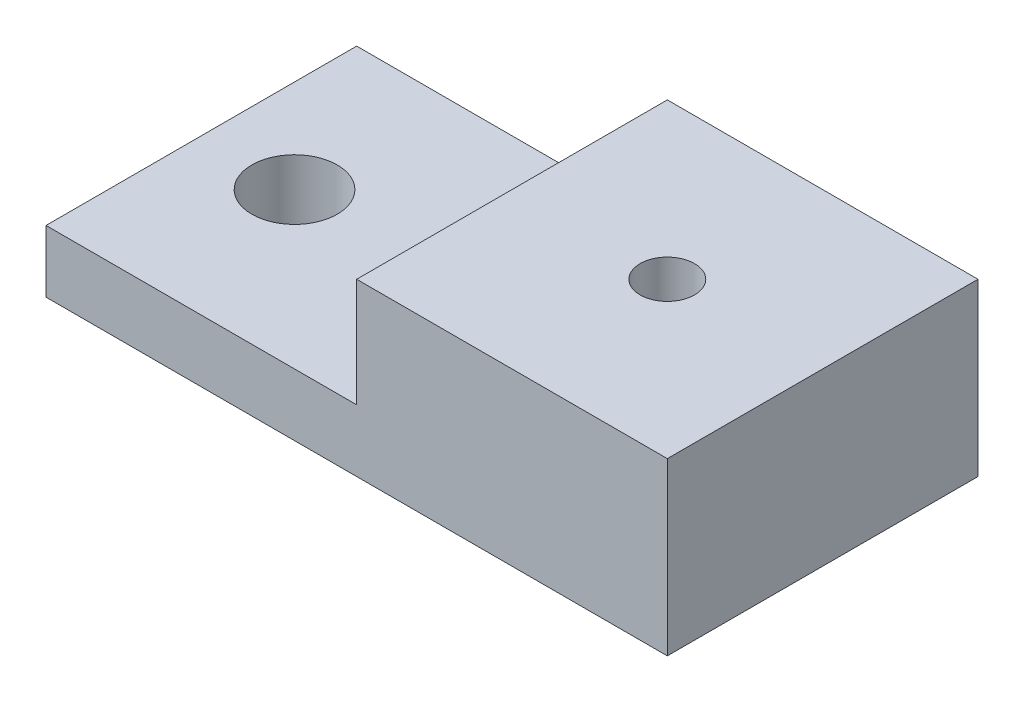
SolidWorks part; units mm, degrees
ref_plane "Front Plane" through (0, 0, 0) normal (0, 0, 1) x (1, 0, 0)
ref_plane "Top Plane" through (0, 0, 0) normal (0, 1, 0) x (1, 0, 0)
ref_plane "Right Plane" through (0, 0, 0) normal (1, 0, 0) x (0, 0, -1)
sketch "Sketch1" plane through (0, 0, 0) normal (0, 1, 0) x (1, 0, 0)
  line L0 (0, 10) -> (40, 10) construction
  line L1 (0, 0) -> (40, 0)
  line L2 (0, 0) -> (0, 20)
  line L3 (0, 20) -> (40, 20)
  line L4 (40, 0) -> (40, 20)
  circle A0 centre (6, 10) radius 2.75
  dimension "D1" = 5.5
  dimension "D4" = 6
  dimension "D2" = 40
  dimension "D3" = 20
extrude "Boss-Extrude1" add sketch "Sketch1" along normal blind 4
sketch "Sketch2" plane through (0, 4, 0) normal (0, 1, 0) x (1, 0, 0)
  line L0 (0, 0) -> (40, 0) construction
  line L1 (40, 20) -> (20, 20)
  line L2 (40, 20) -> (40, 0)
  line L3 (40, 0) -> (20, 0)
  line L4 (20, 20) -> (20, 0)
  dimension "D1" = 20
extrude "Boss-Extrude2" add sketch "Sketch2" along normal blind 7
sketch "Sketch3" plane through (0, 11, 0) normal (0, 1, 0) x (1, 0, 0)
  line L0 (20, 0) -> (40, 20) construction
  circle A0 centre (30, 10) radius 1.75
  dimension "D1" = 3.5
extrude "Cut-Extrude1" cut sketch "Sketch3" against normal through all
sketch "Sketch4" plane through (0, 0, 0) normal (0, -1, 0) x (-1, 0, 0)
  line L0 (-40, 0) -> (-40, 20) construction
  line L1 (-30, 13.2187) -> (-32.7875, 11.6094)
  line L2 (-32.7875, 11.6094) -> (-32.7875, 8.3906)
  line L3 (-32.7875, 8.3906) -> (-30, 6.7813)
  line L4 (-30, 6.7813) -> (-27.2125, 8.3906)
  line L5 (-27.2125, 8.3906) -> (-27.2125, 11.6094)
  line L6 (-27.2125, 11.6094) -> (-30, 13.2187)
  circle A0 centre (-30, 10) radius 2.7875 construction
  circle A1 centre (-30, 10) radius 1.75 construction
  dimension "D1" = 5.575
extrude "Cut-Extrude2" cut sketch "Sketch4" against normal blind 7
